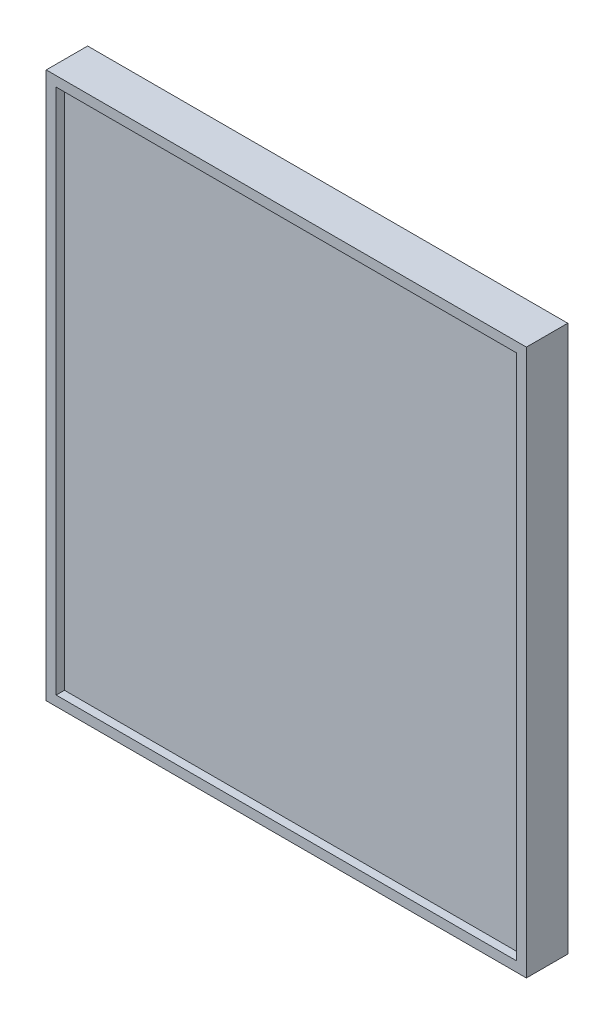
SolidWorks part; units mm, degrees
ref_plane "Front Plane" through (0, 0, 0) normal (0, 0, 1) x (1, 0, 0)
ref_plane "Top Plane" through (0, 0, 0) normal (0, 1, 0) x (1, 0, 0)
ref_plane "Right Plane" through (0, 0, 0) normal (1, 0, 0) x (0, 0, -1)
sketch "Sketch1" plane through (0, 0, 0) normal (0, 0, 1) x (1, 0, 0)
  line L1 (-145, -165) -> (145, -165)
  line L2 (-145, -165) -> (-145, 165)
  line L3 (-145, 165) -> (145, 165)
  line L4 (145, -165) -> (145, 165)
  line L5 (-145, -165) -> (145, 165) construction
  line L6 (-145, 165) -> (145, -165) construction
  point P0 (0, 0)
extrude "Boss-Extrude2" add sketch "Sketch1" along normal blind 25 contours L2 L1 L4 L3
sketch "Sketch7" plane through (0, 0, 25) normal (0, 0, 1) x (1, 0, 0)
  line L1 (-139, -159) -> (139, -159)
  line L2 (-139, -159) -> (-139, 159)
  line L3 (-139, 159) -> (139, 159)
  line L4 (139, -159) -> (139, 159)
  line L5 (-139, -159) -> (139, 159) construction
  line L6 (-139, 159) -> (139, -159) construction
  point P0 (0, 0)
extrude "Cut-Extrude3" cut sketch "Sketch7" against normal blind 5 contours L2 L1 L4 L3
